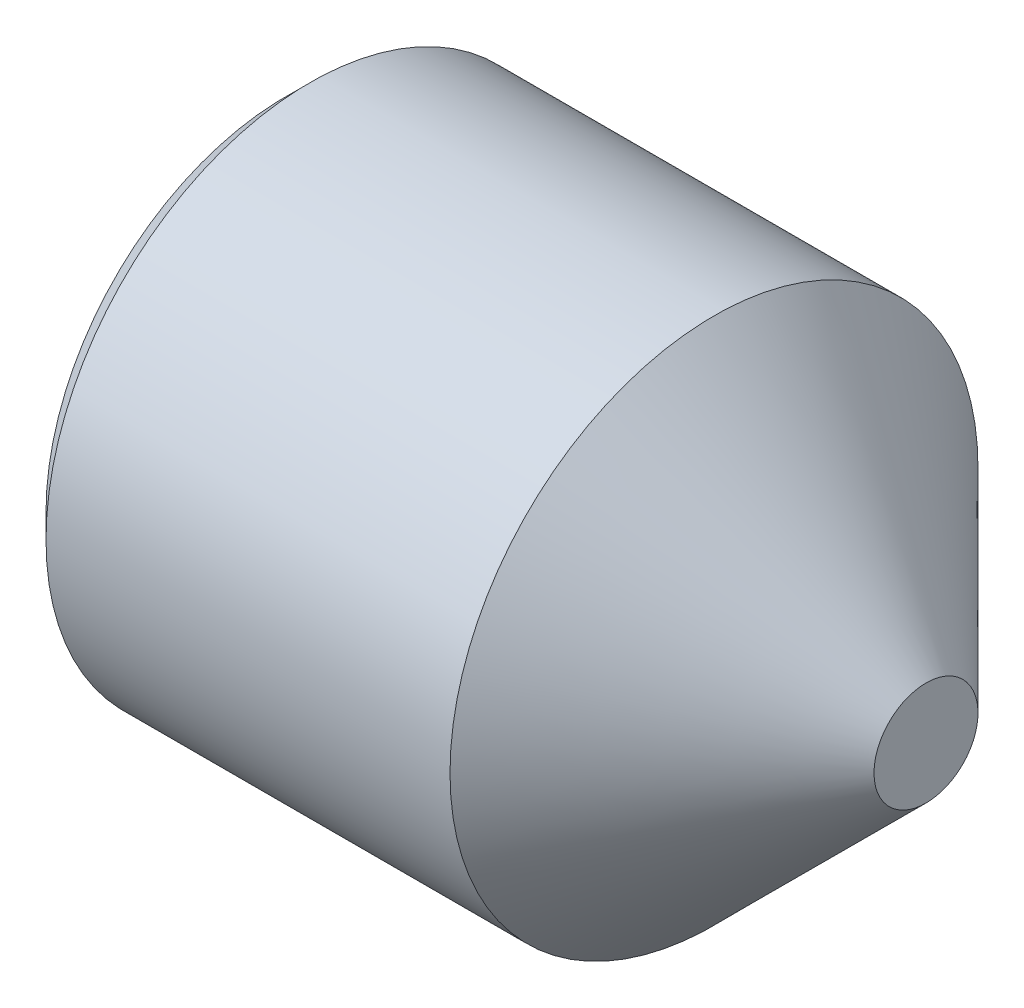
SolidWorks part; units mm, degrees
ref_plane "Front" through (0, 0, 0) normal (0, 0, 1) x (1, 0, 0)
ref_plane "Top" through (0, 0, 0) normal (0, 1, 0) x (1, 0, 0)
ref_plane "Right" through (0, 0, 0) normal (1, 0, 0) x (0, 0, -1)
sketch "Sketch1" plane through (0, 0, 0) normal (0, 0, 1) x (1, 0, 0)
  line L0 (0, 0) -> (4, 0)
  line L1 (4, 0) -> (4, 0.325)
  line L2 (4, 0.325) -> (2.675, 1.65)
  line L3 (2.675, 1.65) -> (0.15, 1.65)
  line L4 (0.15, 1.65) -> (0, 1.5)
  line L5 (0, 1.5) -> (0, 0)
  line L6 (-14.7741, 0) -> (12.5137, 0) construction
  dimension "l" = 4
  dimension "dt" = 0.65
  dimension "d" = 3.3
  dimension "df" = 3
  dimension "D1" = 45
  dimension "D2" = 45
revolve "Base" add sketch "Sketch1" angle 360 about L6
cosmetic thread "ThreadCosmetic1" [suppressed] parameters "D2"=3
sketch "Sketch2" plane through (0, 0.2203, -0.1392) normal (-1, 0, 0) x (0, 0, 1)
  line L1 (0.8898, -0.2203) -> (0.5145, 0.4297)
  line L2 (0.5145, 0.4297) -> (-0.2361, 0.4297)
  line L3 (-0.2361, 0.4297) -> (-0.6114, -0.2203)
  line L4 (-0.6114, -0.2203) -> (-0.2361, -0.8703)
  line L5 (-0.2361, -0.8703) -> (0.5145, -0.8703)
  line L6 (0.5145, -0.8703) -> (0.8898, -0.2203)
  circle A0 centre (0.1392, -0.2203) radius 0.65 construction
  dimension "s" = 1.3
extrude "HexagonSocket" cut sketch "Sketch2" against normal blind 1.2
sketch "Sketch3" plane through (0, 0, 0) normal (0, 0, 1) x (1, 0, 0)
  line L0 (1.2, 0) -> (-2.4777, 0) construction
  line L2 (1.2, 0.65) -> (1.5753, 0)
  line L3 (1.5753, 0) -> (1.2, -0.65) construction
  line L4 (1.2, 0.65) -> (1.2, 0)
  line L5 (1.2, 0) -> (1.5753, 0)
  dimension "D1" = 120
revolve "Cut-Revolve" cut sketch "Sketch3" angle 360 about L0
sketch "Sketch4" plane through (0, 0, 0) normal (0, 0, 1) x (1, 0, 0)
  line L0 (0.15, 1.5201) -> (0.225, 1.65)
  line L1 (0.225, 1.65) -> (0.225, 1.8)
  line L2 (0.225, 1.8) -> (0.075, 1.8)
  line L3 (0.075, 1.8) -> (0.075, 1.65)
  line L4 (0.075, 1.65) -> (0.15, 1.5201)
  line L5 (0, 0) -> (3.2295, 0) construction
  line L6 (0.15, 1.65) -> (0.15, -1.65) construction
  dimension "D1" = 3.3
  dimension "D2" = 0.15
revolve "Cut-Revolve10" [suppressed] cut sketch "Sketch4" angle 360 about L5
pattern_linear "LPattern10" [suppressed] count 22 spacing 0.18 along (1, 0, 0)
equation "\"df@Sketch1\" = \"D2@ThreadCosmetic1\""
equation "\"D1@Sketch4\" = \"d@Sketch1\""
equation "\"D2@Sketch4\" =  ( \"d@Sketch1\" - \"D2@ThreadCosmetic1\" )  / 2"
equation "\"D3@LPattern10\" = \"D2@Sketch4\" * 1.2"
equation "\"D1@LPattern10\" = \"l@Sketch1\" / \"D3@LPattern10\""
